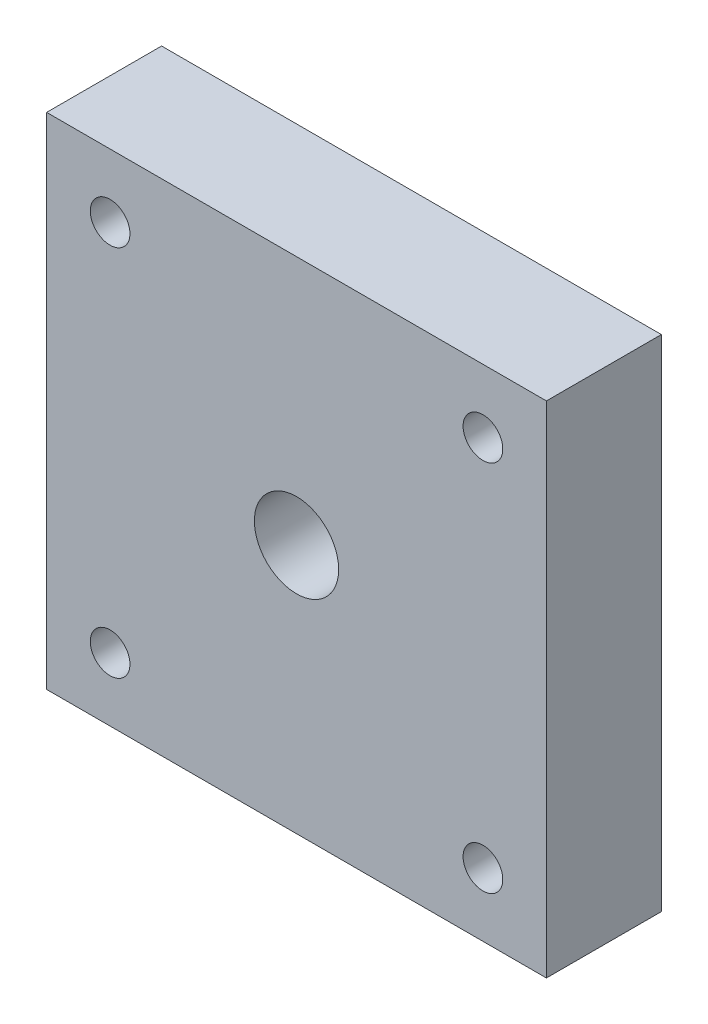
SolidWorks part; units mm, degrees
ref_plane "Front Plane" through (0, 0, 0) normal (0, 0, 1) x (1, 0, 0)
ref_plane "Top Plane" through (0, 0, 0) normal (0, 1, 0) x (1, 0, 0)
ref_plane "Right Plane" through (0, 0, 0) normal (1, 0, 0) x (0, 0, -1)
sketch "Sketch1" plane through (0, 0, 0) normal (0, 0, 1) x (1, 0, 0)
  line L0 (0, 25) -> (0, -25) construction
  line L1 (-25, 0) -> (25, 0) construction
  line L3 (25, -25) -> (-25, -25)
  line L4 (25, -25) -> (25, 25)
  line L5 (25, 25) -> (-25, 25)
  line L6 (-25, -25) -> (-25, 25)
  line L7 (25, -25) -> (-25, 25) construction
  line L8 (25, 25) -> (-25, -25) construction
  point P0 (0, 0)
  point P4 (0, 0)
  point P8 (0, 0)
  dimension "D1" = 50
  dimension "D2" = 50
extrude "Boss-Extrude1" add sketch "Sketch1" along normal blind 11.5
sketch "Sketch2" plane through (0, 0, 11.5) normal (0, 0, 1) x (1, 0, 0)
  line L0 (25, 25) -> (-25, 25) construction
  line L1 (-25, 25) -> (-25, -25) construction
  circle A0 centre (-18.65, 18.65) radius 1.9844
  dimension "D3" = 3.9688
  dimension "D1" = 6.35
  dimension "D2" = 6.35
extrude "Cut-Extrude1" cut sketch "Sketch2" against normal through all
mirror "Mirror1" about plane through (0, 0, 0) normal (0, 1, 0) of "Cut-Extrude1"
mirror "Mirror2" about plane through (0, 0, 0) normal (1, 0, 0) of "Mirror1", "Cut-Extrude1"
sketch "Sketch3" plane through (0, 0, 11.5) normal (0, 0, 1) x (1, 0, 0)
  circle A0 centre (0, 0) radius 4.2164
  dimension "D1" = 8.4328
extrude "Cut-Extrude2" cut sketch "Sketch3" against normal through all
